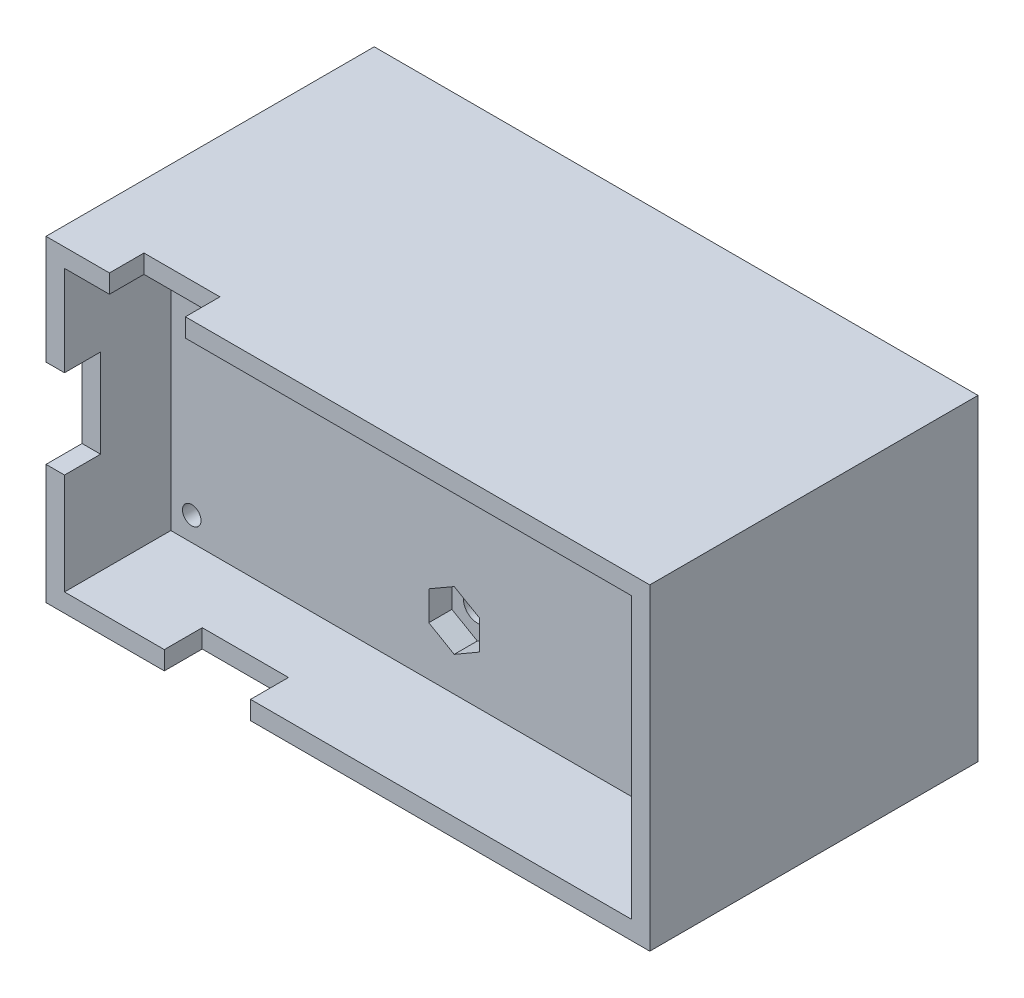
SolidWorks part; units mm, degrees
ref_plane "前视基准面" through (0, 0, 0) normal (0, 0, 1) x (1, 0, 0)
ref_plane "上视基准面" through (0, 0, 0) normal (0, 1, 0) x (1, 0, 0)
ref_plane "右视基准面" through (0, 0, 0) normal (1, 0, 0) x (0, 0, -1)
ref_plane "基准面1" through (0, 0, 3.6001) normal (0, 0, 1) x (1, 0, 0)
sketch "草图1" plane through (0, 0, 3.6001) normal (0, 0, 1) x (1, 0, 0)
  line L0 (0.8763, -38.7224) -> (-59.4234, -38.7224) construction
  line L1 (-48.7034, -33.8618) -> (-39.801, -33.8618)
  line L2 (-48.7034, -33.8618) -> (-48.7034, -38.7224)
  line L4 (-39.801, -33.8618) -> (-39.801, -38.7224)
  line L5 (-59.4234, -9.4107) -> (0.8763, -9.4107) construction
  line L7 (-55.7687, -9.4107) -> (-55.7687, -14.2907)
  line L8 (-55.7687, -14.2907) -> (-45.8066, -14.2907)
  line L9 (-45.8066, -9.4107) -> (-45.8066, -14.2907)
  line L10 (-12.699, -17.609) -> (-12.699, -12.109) construction
  line L11 (0.8763, -9.4107) -> (-45.8066, -9.4107)
  line L12 (0.8763, -9.4107) -> (0.8763, -38.7224)
  line L13 (0.8763, -38.7224) -> (-39.801, -38.7224)
  line L14 (-59.4234, -9.4107) -> (-59.4234, -19.2521)
  line L15 (-29.2736, -33.0846) -> (-20.6538, -33.0846)
  line L16 (-29.2736, -33.0846) -> (-29.2736, -36.2921)
  line L17 (-29.2736, -36.2921) -> (-20.6538, -36.2921)
  line L18 (-20.6538, -33.0846) -> (-20.6538, -36.2921)
  line L23 (-12.699, -12.109) -> (-9.399, -12.109)
  line L24 (-12.699, -12.109) -> (-12.699, -17.609)
  line L25 (-12.699, -17.609) -> (-9.399, -17.609)
  line L26 (-9.399, -12.109) -> (-9.399, -17.609)
  line L27 (-48.7034, -38.7224) -> (-59.4234, -38.7224)
  line L28 (-55.7687, -9.4107) -> (-59.4234, -9.4107)
  line L29 (-59.4234, -27.6866) -> (-59.4234, -38.7224)
  line L30 (-59.4234, -19.2521) -> (-54.3557, -19.2521)
  line L32 (-59.4234, -27.6866) -> (-54.3557, -27.6866)
  line L33 (-54.3557, -19.2521) -> (-54.3557, -27.6866)
  circle A0 centre (-57.6581, -36.6498) radius 1
  circle A1 centre (-57.6581, -11.2498) radius 1
  circle A2 centre (-1.016, -11.2498) radius 1
  circle A3 centre (-0.889, -36.8301) radius 1
  circle A4 centre (-4.1259, -29.4689) radius 1.322
  circle A5 centre (-5.9082, -27.2775) radius 0.4462
  circle A6 centre (-4.5737, -26.6799) radius 0.4462
  circle A7 centre (-3.1192, -26.8297) radius 0.4462
  circle A8 centre (-1.9345, -27.6866) radius 0.4462
  circle A9 centre (-1.3369, -29.0211) radius 0.4462
  circle A10 centre (-1.4866, -30.4756) radius 0.4462
  circle A11 centre (-2.3435, -31.6603) radius 0.4462
  circle A12 centre (-3.678, -32.2579) radius 0.4462
  circle A13 centre (-5.1325, -32.1082) radius 0.4462
  circle A14 centre (-6.3173, -31.2513) radius 0.4462
  circle A15 centre (-6.9149, -29.9168) radius 0.4462
  circle A16 centre (-6.7652, -28.4623) radius 0.4462
  point P71 (-4.1259, -29.4689)
  dimension "D1" = 12
ref_plane "基准面2" through (0, 0, -6) normal (0, 0, -1) x (-1, 0, 0)
sketch "草图2" plane through (0, 0, -6) normal (0, 0, -1) x (-1, 0, 0)
  line L0 (29.2736, -9.4107) -> (29.2736, -29.309) construction
  line L1 (-0.8763, -38.7224) -> (59.4234, -38.7224)
  line L2 (-0.8763, -38.7224) -> (-0.8763, -9.4107)
  line L3 (-0.8763, -9.4107) -> (59.4234, -9.4107)
  line L4 (59.4234, -38.7224) -> (59.4234, -9.4107)
  line L5 (59.4234, -24.0665) -> (-9.3078, -24.0665) construction
  line L9 (29.2736, -15.8165) -> (29.2736, -13.1836) construction
  line L10 (27.7854, -15.8165) -> (27.7854, -13.1836)
  line L11 (30.7617, -15.8165) -> (30.7617, -13.1836)
  line L12 (29.2736, -38.7224) -> (29.2736, -43.3487) construction
  line L14 (-3.3763, -6.9107) -> (61.9234, -6.9107)
  line L15 (-3.3763, -6.9107) -> (-3.3763, -41.2224)
  line L16 (-3.3763, -41.2224) -> (61.9234, -41.2224)
  line L17 (61.9234, -6.9107) -> (61.9234, -41.2224)
  circle A0 centre (1.016, -11.2498) radius 1
  circle A1 centre (0.889, -36.8301) radius 1
  circle A2 centre (57.6581, -36.6498) radius 1
  circle A3 centre (57.6581, -11.2498) radius 0.9222
  arc A10 (27.7854, -15.8165) -> (30.7617, -15.8165) centre (29.2736, -15.8165) ccw
  arc A11 (30.7617, -13.1836) -> (27.7854, -13.1836) centre (29.2736, -13.1836) ccw
  circle A12 centre (29.2736, -32.3165) radius 1.5
  point P27 (29.2736, -31.5665)
  point P33 (29.2736, -14.5001)
  dimension "D1" = 2.5
  dimension "D2" = 2.5
  dimension "D3" = 3
  dimension "D4" = 8.25
  dimension "D5" = 2.5
  dimension "D6" = 2.5
  dimension "D7" = 8.25
extrude "凸台-拉伸2" add sketch "草图2" along normal blind 4.5 separate body
sketch "草图3" plane through (0, 0, -6) normal (0, 0, -1) x (-1, 0, 0)
  line L0 (29.2736, -15.8165) -> (29.2736, -10.8487) construction
  line L1 (32.0236, -17.4043) -> (32.0236, -14.2288)
  line L4 (26.5236, -14.2288) -> (26.5236, -17.4043)
  line L5 (26.5236, -17.4043) -> (29.2736, -18.992)
  line L6 (29.2736, -18.992) -> (32.0236, -17.4043)
  line L8 (32.0236, -14.9203) -> (32.0236, -11.7449)
  line L9 (32.0236, -11.7449) -> (29.2736, -10.1572)
  line L10 (29.2736, -10.1572) -> (26.5236, -11.7449)
  line L11 (26.5236, -11.7449) -> (26.5236, -14.9203)
  line L14 (31.8974, -14.9932) -> (32.0236, -14.9203) [skipped]
  line L15 (29.2736, -22.4541) -> (17.663, -22.4541) construction
  line L16 (29.2736, -22.4541) -> (29.2736, -17.3047) construction
  line L17 (26.6497, -14.156) -> (26.5236, -14.2288) [skipped]
  line L18 (26.5236, -14.9203) -> (26.6497, -14.9932) [skipped]
  line L19 (32.0236, -14.2288) -> (31.8974, -14.156) [skipped]
  line L20 (26.5236, -33.9043) -> (29.2736, -35.492)
  line L21 (29.2736, -35.492) -> (32.0236, -33.9043)
  line L22 (32.0236, -33.9043) -> (32.0236, -30.7288)
  line L23 (32.0236, -30.7288) -> (29.2736, -29.1411)
  line L24 (29.2736, -29.1411) -> (26.5236, -30.7288)
  line L25 (26.5236, -30.7288) -> (26.5236, -33.9043)
  arc A0 (26.82, -14.5746) -> (31.7271, -14.5746) centre (29.2736, -15.8165) ccw construction
  arc A1 (31.7271, -14.5746) -> (26.82, -14.5746) centre (29.2736, -13.3326) ccw construction
  circle A2 centre (29.2736, -32.3165) radius 2.75 construction
  arc A5 (27.7854, -15.8165) -> (30.7617, -15.8165) centre (29.2736, -15.8165) ccw construction
  point P25 (29.2736, -33.8241)
  dimension "D1" = 5.5
extrude "切除-拉伸2" cut sketch "草图3" along normal blind 2.5 contours L10 L11 L4 L5 L6 L1 L8 L9 | L24 L25 L20 L21 L22 L23
sketch "草图5" plane through (0, 0, -10.5) normal (0, 0, -1) x (-1, 0, 0)
  line L1 (-3.3763, -6.9107) -> (61.9234, -6.9107)
  line L2 (-3.3763, -6.9107) -> (-3.3763, -41.2224)
  line L3 (-3.3763, -41.2224) -> (61.9234, -41.2224)
  line L4 (61.9234, -6.9107) -> (61.9234, -41.2224)
  line L5 (-1.3763, -8.9107) -> (59.9234, -8.9107)
  line L6 (-1.3763, -8.9107) -> (-1.3763, -39.2224)
  line L7 (-1.3763, -39.2224) -> (59.9234, -39.2224)
  line L8 (59.9234, -8.9107) -> (59.9234, -39.2224)
  dimension "D1" = 2
  dimension "D2" = 2
  dimension "D3" = 2
  dimension "D4" = 2
extrude "凸台-拉伸3" add sketch "草图5" along normal blind 15.5 and the other way blind 16
sketch "草图7" plane through (0, -6.9107, 0) normal (0, 1, 0) x (1, 0, 0)
  line L0 (-41.7981, -5.5601) -> (-46.8481, -5.5601) construction
  line L1 (-55.0622, -1.765) -> (-46.8481, -1.765)
  line L2 (-55.0622, -1.765) -> (-55.0622, -5.5601)
  line L3 (-55.0622, -5.5601) -> (-46.8481, -5.5601)
  line L4 (-46.8481, -1.765) -> (-46.8481, -5.5601)
extrude "切除-拉伸4" cut sketch "草图7" against normal blind 3
sketch "草图8" plane through (-61.9234, 0, 0) normal (-1, 0, 0) x (0, 0, 1)
  line L0 (5.6001, -27.6866) -> (5.6001, -38.7224) construction
  line L1 (1.6001, -18.6953) -> (5.6001, -18.6953)
  line L2 (1.6001, -18.6953) -> (1.6001, -28.2708)
  line L3 (1.6001, -28.2708) -> (5.6001, -28.2708)
  line L4 (5.6001, -18.6953) -> (5.6001, -28.2708)
  dimension "D1" = 4
extrude "切除-拉伸5" cut sketch "草图8" against normal blind 3
sketch "草图9" plane through (0, -41.2224, 0) normal (0, -1, 0) x (1, 0, 0)
  line L0 (-59.4234, 5.6001) -> (-48.7034, 5.6001) construction
  line L1 (-49.1273, 5.6001) -> (-39.801, 5.6001)
  line L2 (-49.1273, 5.6001) -> (-49.1273, 1.3978)
  line L3 (-49.1273, 1.3978) -> (-39.801, 1.3978)
  line L4 (-39.801, 5.6001) -> (-39.801, 1.3978)
extrude "切除-拉伸6" cut sketch "草图9" against normal blind 3
sketch "草图10" plane through (0, 0, -26) normal (0, 0, -1) x (-1, 0, 0)
  line L0 (29.2736, -8.9107) -> (29.2736, -43.7563) construction
  line L1 (-3.3763, -6.9107) -> (61.9234, -6.9107)
  line L2 (-3.3763, -6.9107) -> (-3.3763, -41.2224)
  line L3 (-3.3763, -41.2224) -> (61.9234, -41.2224)
  line L4 (61.9234, -6.9107) -> (61.9234, -41.2224)
  line L5 (-1.3763, -8.9107) -> (59.9234, -8.9107)
  line L6 (-1.3763, -8.9107) -> (-1.3763, -39.2224)
  line L7 (-1.3763, -39.2224) -> (59.9234, -39.2224)
  line L8 (59.9234, -8.9107) -> (59.9234, -39.2224)
  line L9 (-1.3763, -24.0665) -> (74.3166, -24.0665) construction
  circle A0 centre (1.016, -11.2498) radius 1
  arc A1 (-1.3763, -14.9107) -> (4.6237, -8.9107) centre (-1.3763, -8.9107) ccw
  circle A2 centre (57.6581, -11.2498) radius 1
  arc A3 (53.9234, -8.9107) -> (59.9234, -14.9107) centre (59.9234, -8.9107) ccw
  circle A4 centre (57.6581, -36.8833) radius 1
  arc A5 (53.9234, -39.2224) -> (59.9234, -33.2224) centre (59.9234, -39.2224) cw
  circle A6 centre (1.016, -36.8833) radius 1
  arc A7 (-1.3763, -33.2224) -> (4.6237, -39.2224) centre (-1.3763, -39.2224) cw
  line M2 (-3.3763, -6.9107) -> (-3.3763, -41.2224)
  line M3 (-3.3763, -41.2224) -> (61.9234, -41.2224)
  line M4 (61.9234, -41.2224) -> (61.9234, -6.9107)
  line M5 (61.9234, -6.9107) -> (-3.3763, -6.9107)
  line M6 (59.9234, -39.2224) -> (-1.3763, -39.2224)
  line M7 (-1.3763, -39.2224) -> (-1.3763, -8.9107)
  line M8 (-1.3763, -8.9107) -> (59.9234, -8.9107)
  line M9 (59.9234, -8.9107) -> (59.9234, -39.2224)
  dimension "D1" = 6
  dimension "D2" = 6
  dimension "D3" = 2
  dimension "D4" = 2
extrude "凸台-拉伸4" add sketch "草图10" along normal blind 4 contours L8 L7 L6 L5 M5 M2 M3 M4 M9 M6 M7 M8 | L6 A1 A0 M8 | A7 A6 M7 M6 | A5 A4 M6 M9 | A3 A2 M8 M9
sketch "草图11" plane through (0, 0, -30) normal (0, 0, -1) x (-1, 0, 0)
  line L1 (-3.3763, -6.9107) -> (61.9234, -6.9107)
  line L2 (-3.3763, -6.9107) -> (-3.3763, -41.2224)
  line L3 (-3.3763, -41.2224) -> (61.9234, -41.2224)
  line L4 (61.9234, -6.9107) -> (61.9234, -41.2224)
  circle A0 centre (1.016, -11.2498) radius 1
  circle A1 centre (1.016, -36.8833) radius 1
  circle A2 centre (57.6581, -36.8833) radius 1
  circle A3 centre (57.6581, -11.2498) radius 1
